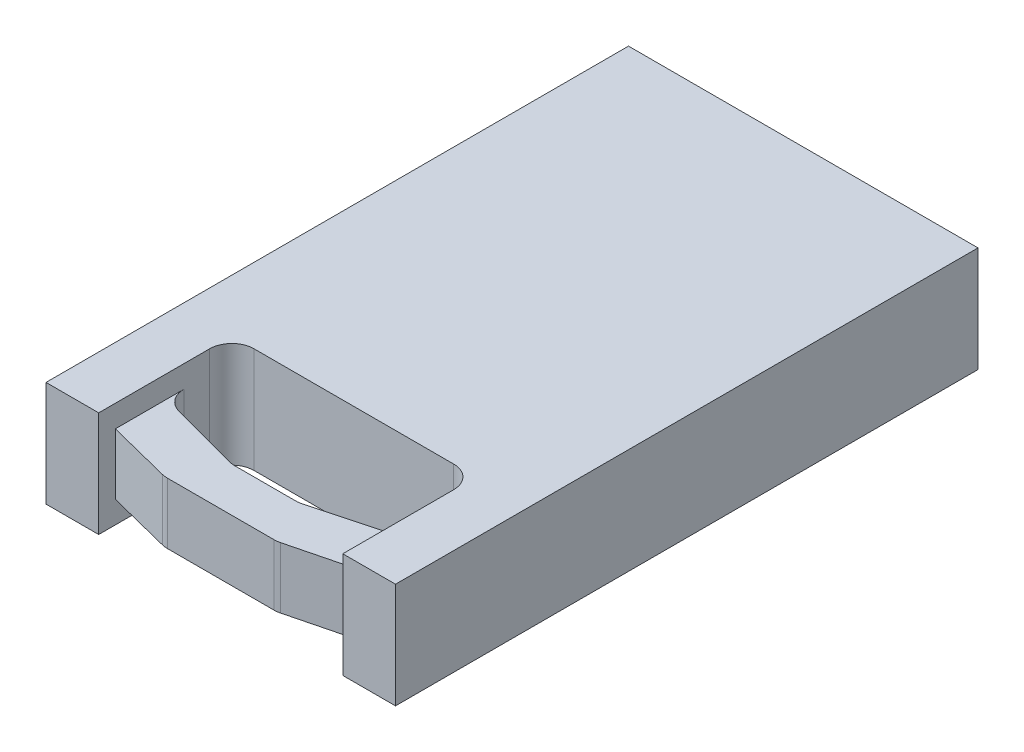
SolidWorks part; units mm, degrees
ref_plane "Front Plane" through (0, 0, 0) normal (0, 0, 1) x (1, 0, 0)
ref_plane "Top Plane" through (0, 0, 0) normal (0, 1, 0) x (1, 0, 0)
ref_plane "Right Plane" through (0, 0, 0) normal (1, 0, 0) x (0, 0, -1)
sketch "Sketch1" plane through (0, 0, 0) normal (0, 1, 0) x (1, 0, 0)
  line L1 (-209.55, -166.6875) -> (209.55, -166.6875)
  line L2 (-209.55, -166.6875) -> (-209.55, 166.6875)
  line L3 (-209.55, 166.6875) -> (209.55, 166.6875)
  line L4 (209.55, -166.6875) -> (209.55, 166.6875)
  line L5 (-209.55, -166.6875) -> (209.55, 166.6875) construction
  line L6 (-209.55, 166.6875) -> (209.55, -166.6875) construction
  point P0 (0, 0)
  dimension "D1" = 333.375
  dimension "D2" = 419.1
extrude "Boss-Extrude1" add sketch "Sketch1" along normal blind 60.325
sketch "Sketch2" plane through (0, 60.325, 0) normal (0, 1, 0) x (1, 0, 0)
  line L0 (0, 0) -> (0, -115.8875) construction
  line L1 (-69.85, -141.2875) -> (69.85, -141.2875)
  line L2 (-69.85, -141.2875) -> (-69.85, -90.4875)
  line L3 (-69.85, -90.4875) -> (69.85, -90.4875)
  line L4 (69.85, -141.2875) -> (69.85, -90.4875)
  line L5 (-69.85, -141.2875) -> (69.85, -90.4875) construction
  line L6 (-69.85, -90.4875) -> (69.85, -141.2875) construction
  line L7 (-209.55, -166.6875) -> (209.55, -166.6875) construction
  line L8 (-69.85, -166.6875) -> (-69.85, -157.1625)
  line L9 (-69.85, -157.1625) -> (-32.169, -166.6875)
  line L10 (-32.169, -166.6875) -> (-69.85, -166.6875)
  line L11 (-69.85, -157.1625) -> (-69.85, -141.2875) construction
  line L12 (0, -166.6875) -> (0, -141.2875) construction
  line L13 (69.85, -157.1625) -> (69.85, -141.2875) construction
  line L14 (32.169, -166.6875) -> (69.85, -166.6875)
  line L15 (69.85, -157.1625) -> (32.169, -166.6875)
  line L16 (69.85, -166.6875) -> (69.85, -157.1625)
  point P0 (0, -115.8875)
  dimension "D1" = 139.7
  dimension "D2" = 50.8
  dimension "D3" = 50.8
  dimension "D4" = 9.525
extrude "Cut-Extrude1" cut sketch "Sketch2" against normal through all
chamfer "Chamfer1" distance 50.8 angle 15 2 edges at (69.85, 30.1625, 141.2875) (-69.85, 30.1625, 141.2875)
fillet "Fillet1" radius 12.7 8 edges at (32.169, 30.1625, 166.6875) (-32.169, 30.1625, 166.6875) (69.85, 30.1625, 127.6757) (19.05, 30.1625, 141.2875) (-19.05, 30.1625, 141.2875) (-69.85, 30.1625, 127.6757) (69.85, 30.1625, 90.4875) (-69.85, 30.1625, 90.4875)
sketch "Sketch3" plane through (0, 60.325, 0) normal (0, 1, 0) x (1, 0, 0)
  line L1 (-69.85, -166.6875) -> (69.85, -166.6875)
  line L2 (-69.85, -166.6875) -> (-69.85, -110.2845)
  line L3 (-69.85, -110.2845) -> (69.85, -110.2845)
  line L4 (69.85, -166.6875) -> (69.85, -110.2845)
extrude "Cut-Extrude2" cut sketch "Sketch3" against normal blind 12.7
sketch "Sketch4" plane through (0, 0, 0) normal (0, -1, 0) x (1, 0, 0)
  line L0 (69.85, 117.9306) -> (69.85, 103.1875) construction
  line L1 (-69.85, 166.6875) -> (69.85, 166.6875)
  line L2 (-69.85, 166.6875) -> (-69.85, 110.5591)
  line L3 (-69.85, 110.5591) -> (69.85, 110.5591)
  line L4 (69.85, 166.6875) -> (69.85, 110.5591)
extrude "Cut-Extrude3" cut sketch "Sketch4" against normal blind 12.7
sketch "Sketch5" plane through (0, 60.325, 0) normal (0, 1, 0) x (1, 0, 0)
  line L0 (209.55, 166.6875) -> (-209.55, 166.6875) construction
  line L1 (-100.0125, -166.6875) -> (100.0125, -166.6875)
  line L2 (-100.0125, -166.6875) -> (-100.0125, 166.6875)
  line L3 (-100.0125, 166.6875) -> (100.0125, 166.6875)
  line L4 (100.0125, -166.6875) -> (100.0125, 166.6875)
  line L5 (-100.0125, -166.6875) -> (100.0125, 166.6875) construction
  line L6 (-100.0125, 166.6875) -> (100.0125, -166.6875) construction
  point P0 (0, 0)
  dimension "D1" = 200.025
extrude "Cut-Extrude4" cut sketch "Sketch5" against normal through all flip side to cut
